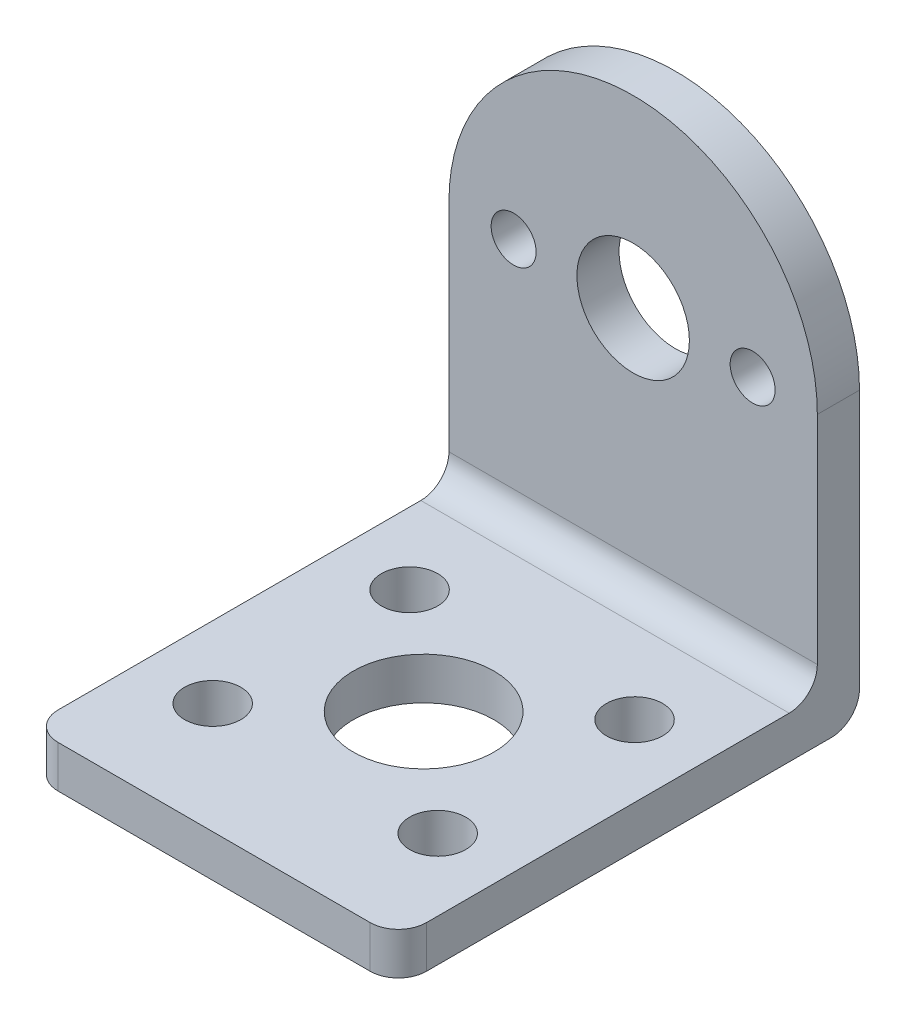
SolidWorks part; units mm, degrees
material "AISI 304"
ref_plane "Front Plane" through (0, 0, 0) normal (0, 0, 1) x (1, 0, 0)
ref_plane "Top Plane" through (0, 0, 0) normal (0, 1, 0) x (1, 0, 0)
ref_plane "Right Plane" through (0, 0, 0) normal (1, 0, 0) x (0, 0, -1)
sketch "Sketch1" plane through (0, 0, 0) normal (0, 0, 1) x (1, 0, 0)
  line L0 (-13.1, 20.4) -> (-13.1, 0)
  line L1 (-13.1, 0) -> (13.1, 0)
  line L2 (13.1, 0) -> (13.1, 20.4)
  line L3 (-8.5, 20.4) -> (8.5, 20.4) construction
  arc A0 (-13.1, 20.4) -> (13.1, 20.4) centre (0, 20.4) cw
  circle A1 centre (0, 20.4) radius 4
  circle A2 centre (-8.5, 20.4) radius 1.6
  circle A3 centre (8.5, 20.4) radius 1.6
  dimension "D2" = 20.4
  dimension "D3" = 3.2
  dimension "D4" = 8
  dimension "D1" = 26.2
  dimension "D5" = 17
extrude "Boss-Extrude1" add sketch "Sketch1" along normal blind 3
sketch "Sketch2" plane through (0, 0, 0) normal (0, -1, 0) x (1, 0, 0)
  line L0 (13.1, 3) -> (-13.1, 3) construction
  line L1 (13.1, 3) -> (-13.1, 3)
  line L2 (13.1, 3) -> (13.1, 32.8)
  line L3 (13.1, 32.8) -> (-13.1, 32.8)
  line L4 (-13.1, 3) -> (-13.1, 32.8)
  line L5 (-13.1, 0) -> (13.1, 0) construction
  line L7 (8, 10.9) -> (-8, 10.9) construction
  line L8 (8, 10.9) -> (8, 24.9) construction
  line L9 (8, 24.9) -> (-8, 24.9) construction
  line L10 (-8, 10.9) -> (-8, 24.9) construction
  line L11 (8, 10.9) -> (-8, 24.9) construction
  line L12 (8, 24.9) -> (-8, 10.9) construction
  circle A0 centre (8, 24.9) radius 2
  circle A1 centre (8, 10.9) radius 2
  circle A2 centre (-8, 10.9) radius 2
  circle A3 centre (-8, 24.9) radius 2
  circle A4 centre (0, 17.9) radius 5
  point P11 (0, 17.9)
  dimension "D2" = 10
  dimension "D3" = 4
  dimension "D1" = 32.8
  dimension "D4" = 7.9
  dimension "D5" = 14
  dimension "D6" = 16
extrude "Boss-Extrude2" add sketch "Sketch2" against normal blind 3
fillet "Fillet1" radius 2 4 edges at (0, 0, 0) (0, 3, 3) (-13.1, 1.5, 32.8) (13.1, 1.5, 32.8)
